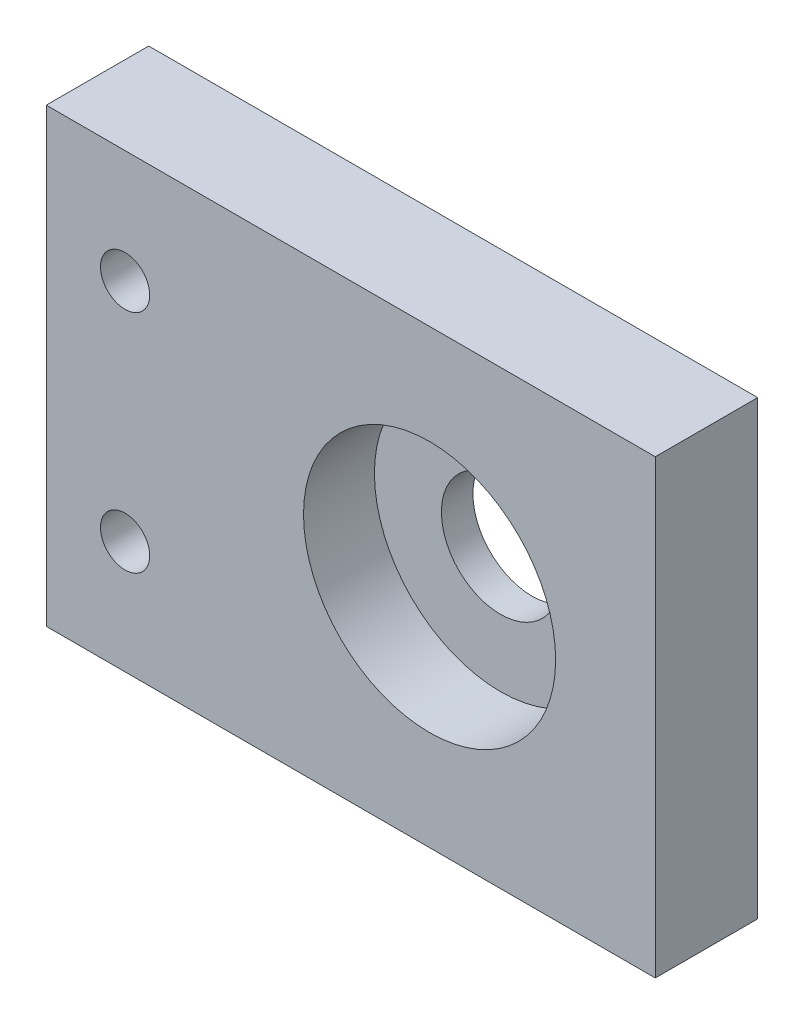
SolidWorks part; units mm, degrees
ref_plane "Front Plane" through (0, 0, 0) normal (0, 0, 1) x (1, 0, 0)
ref_plane "Top Plane" through (0, 0, 0) normal (0, 1, 0) x (1, 0, 0)
ref_plane "Right Plane" through (0, 0, 0) normal (1, 0, 0) x (0, 0, -1)
sketch "Sketch1" plane through (0, 0, 0) normal (0, 0, 1) x (1, 0, 0)
  line L1 (-38.65, -28.65) -> (38.65, -28.65)
  line L2 (-38.65, -28.65) -> (-38.65, 28.65)
  line L3 (-38.65, 28.65) -> (38.65, 28.65)
  line L4 (38.65, -28.65) -> (38.65, 28.65)
  line L5 (-38.65, -28.65) -> (38.65, 28.65) construction
  line L6 (-38.65, 28.65) -> (38.65, -28.65) construction
  point P0 (0, 0)
  dimension "D1" = 57.3
  dimension "D2" = 77.3
extrude "Boss-Extrude1" add sketch "Sketch1" along normal blind 13
sketch "Sketch2" plane through (0, 0, 13) normal (0, 0, 1) x (1, 0, 0)
  line L0 (-18.65, 28.65) -> (-18.65, -28.65) construction
  line L1 (-18.65, 0) -> (10, 0) construction
  line L2 (-28.65, 28.65) -> (-28.65, -28.65) construction
  line L4 (38.65, 28.65) -> (-38.65, 28.65) construction
  line L5 (-38.65, -28.65) -> (38.65, -28.65) construction
  line L6 (-38.65, 28.65) -> (-38.65, -28.65) construction
  circle A5 centre (10, 0) radius 16
  point P22 (-28.65, 14.325)
  point P23 (-28.65, 0)
  point P24 (-28.65, -14.325)
  dimension "D3" = 32
  dimension "D1" = 20
  dimension "D2" = 28.65
  dimension "D10" = 10
hole_wizard "Tap Drill for M6 Helicoil1" positions "3DSketch2" profile "Sketch5" hole size "M6x1.0" standard "ANSI Metric"
sketch3d "3DSketch2"
  point P0 (-28.65, 14.325, 13)
  point P3 (-28.65, -14.325, 13)
sketch "Sketch5" plane through (-28.65, 14.325, 13) normal (1, 0, 0) x (0, -1, 0)
  line L0 (0, 0) -> (0, 21.8777)
  line L1 (0, 21.8777) -> (3.125, 20)
  line L2 (3.125, 20) -> (3.125, 0)
  line L5 (3.125, 0) -> (0, 0)
  line L10 (0, 21.8777) -> (-3.125, 20) construction
  line L11 (0, -6.35) -> (0, 107.95) construction
  dimension "Hole Dia." = 6.25
  dimension "Hole Depth" = 20
  dimension "Drill Angle" = 118
extrude "Cut-Extrude1" cut sketch "Sketch2" against normal blind 9
sketch "Sketch6" plane through (0, 0, 4) normal (0, 0, 1) x (1, 0, 0)
  circle A0 centre (10, 0) radius 7.5
  dimension "D1" = 15
extrude "Cut-Extrude2" cut sketch "Sketch6" against normal blind 9
